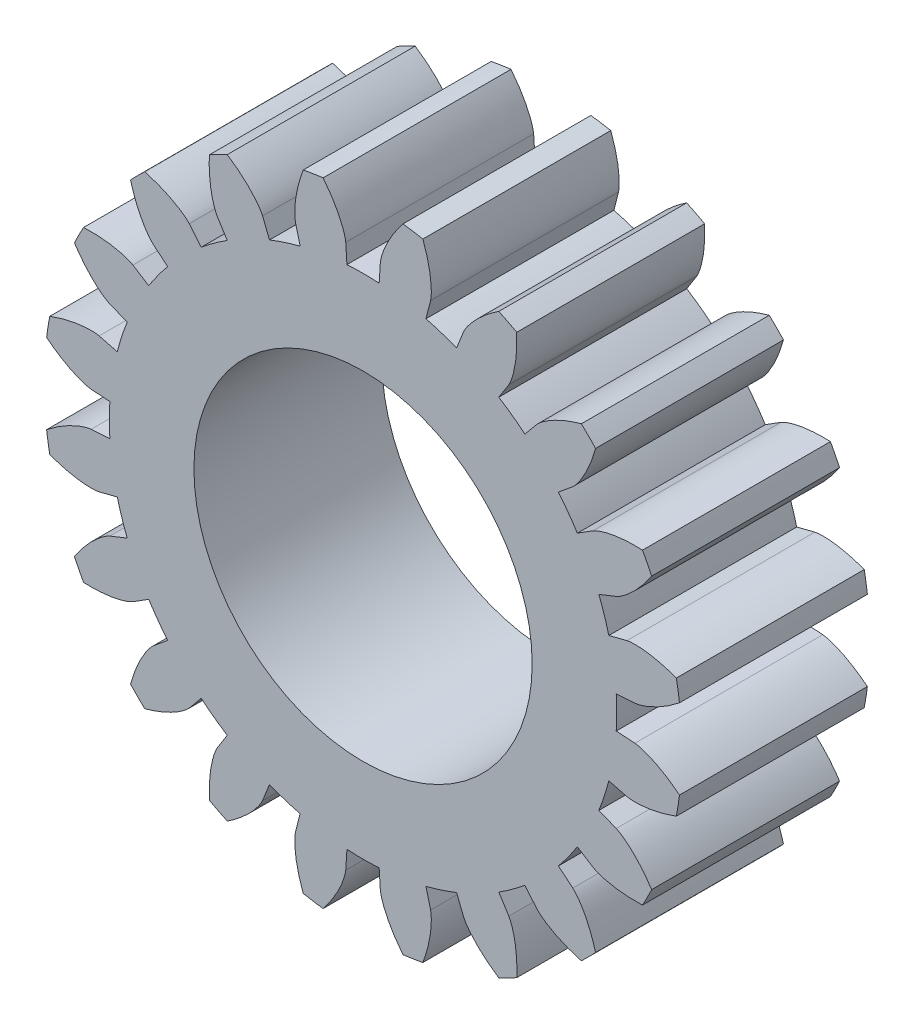
SolidWorks part; units mm, degrees
ref_plane "Front Plane" through (0, 0, 0) normal (0, 0, 1) x (1, 0, 0)
ref_plane "Top Plane" through (0, 0, 0) normal (0, 1, 0) x (1, 0, 0)
ref_plane "Right Plane" through (0, 0, 0) normal (1, 0, 0) x (0, 0, -1)
sketch "Sketch1" plane through (0, 0, 0) normal (0, 0, 1) x (1, 0, 0)
  line L0 (0, 0) -> (0, 16.9725) construction
  line L1 (0, 16.9725) -> (0, 0) construction
  line L2 (0, 0) -> (-16.9725, 0) construction
  circle A0 centre (0, 0) radius 16.9725
  dimension "D1" = 33.945
extrude "Boss-Extrude1" add sketch "Sketch1" along normal blind 10 contours A0
sketch "Sketch3" plane through (0, 0, 10) normal (0, 0, 1) x (1, 0, 0)
  line L0 (0, 0) -> (0, 16.9725) construction
  line L1 (0, 16.9725) -> (0, 0) construction
  line L2 (-16.9725, 0) -> (0, 0) construction
  line L3 (0, 0) -> (-0.9209, 14.4674) construction
  line L4 (0, 0) -> (-2.4281, 14.2919) construction
  line L5 (-2.4281, 14.2919) -> (-0.9314, 14.5462) construction
  line L6 (0, 0) -> (-3.9087, 13.9598) construction
  line L7 (-3.9087, 13.9598) -> (-0.9848, 14.7785) construction
  line L8 (-5.3465, 13.4747) -> (0, 0) construction
  line L9 (0, 0) -> (-5.3465, 13.4747) construction
  line L10 (-5.3465, 13.4747) -> (-1.113, 15.1545) construction
  line L11 (0, 0) -> (-6.7257, 12.8421) construction
  line L12 (-6.7257, 12.8421) -> (-1.3461, 15.6595) construction
  line L13 (0, 0) -> (-8.0312, 12.0687) construction
  line L14 (-8.0312, 12.0687) -> (-1.7117, 16.2741) construction
  line L15 (0, 0) -> (-9.2487, 11.1631) construction
  line L16 (-9.2487, 11.1631) -> (-2.2344, 16.9746) construction
  line L17 (0, 0) -> (-10.3649, 10.1352) construction
  line L18 (-10.3649, 10.1352) -> (-2.9351, 17.7335) construction
  circle A0 centre (0, 0) radius 16.9725 construction
  circle A1 centre (0, 0) radius 14.4967 construction
  circle A2 centre (0, 0) radius 15.4286 construction
  arc A3 (0.5713, 14.5148) -> (-0.9209, 14.4674) centre (0.5713, -8.9752) ccw construction
  arc A4 (0.9209, 14.4674) -> (-0.9209, 14.4674) centre (0, 0) ccw
  arc A5 (-2.9351, 17.7335) -> (2.9351, 17.7335) centre (0, 1.0167) cw
  spline S0 degree 3 poles (-0.9209, 14.4674) (-0.9317, 14.5729) (-0.9862, 14.8058) (-1.125, 15.2067) (-1.3613, 15.7115) (-1.9072, 16.6215) (-2.4816, 17.2888) (-2.9351, 17.7335) knots 0 0 0 0 0.081636 0.183677 0.326533 0.510206 1 1 1 1
  spline S1 degree 3 poles (0.9209, 14.4674) (0.9317, 14.5729) (0.9862, 14.8058) (1.125, 15.2067) (1.3613, 15.7115) (1.9072, 16.6215) (2.4816, 17.2888) (2.9351, 17.7335) knots 0 0 0 0 0.081636 0.183677 0.326533 0.510206 1 1 1 1
  point P13 (-1.2096, 15.3811)
  point P43 (-0.6565, 9.8523)
  dimension "D18" = 30.8571
  dimension "D2" = 28.9933
  dimension "D3" = 1.2096
  dimension "D4" = 6
  dimension "D5" = 1.5182
  dimension "D6" = 6
  dimension "D7" = 3.0363
  dimension "D8" = 4.5545
  dimension "D9" = 6
  dimension "D10" = 6.0727
  dimension "D11" = 6
  dimension "D12" = 6
  dimension "D13" = 7.5909
  dimension "D14" = 6
  dimension "D15" = 9.109
  dimension "D16" = 6
  dimension "D17" = 10.6272
extrude "Cut-Extrude1" cut sketch "Sketch3" against normal blind 10
sketch "Sketch5" plane through (0, 0, 10) normal (0, 0, 1) x (1, 0, 0)
  line L0 (-0.9209, 14.4674) -> (0, 0)
  line L1 (0, 0) -> (0.9209, 14.4674)
  arc A0 (0.9209, 14.4674) -> (-0.9209, 14.4674) centre (0, 0) ccw construction
  arc A1 (0.9209, 14.4674) -> (-0.9209, 14.4674) centre (0, 0) ccw
  circle A2 centre (0, 0) radius 13.5
  arc M7 (0.9209, 14.4674) -> (-0.9209, 14.4674) centre (0, 0) ccw
  dimension "D1" = 27
extrude "Cut-Extrude2" cut sketch "Sketch5" against normal blind 10 contours A2 L1 L0 M7
pattern_circular "CirPattern1" count 20 over 360 about axis through (0, 0, 10) along (0, 0, -1) of "Cut-Extrude1", "Cut-Extrude2"
sketch "Sketch7" plane through (0, 0, 10) normal (0, 0, 1) x (1, 0, 0)
  circle A0 centre (0, 0) radius 9
  dimension "D1" = 18
extrude "Cut-Extrude3" cut sketch "Sketch7" against normal blind 10 contours A0
sketch "Sketch6" plane through (0, 0, 10) normal (0, 0, 1) x (1, 0, 0)
  line L1 (-2.5, 5) -> (2.5, 5)
  line L2 (-2.5, 5) -> (-2.5, 15)
  line L3 (-2.5, 15) -> (2.5, 15)
  line L4 (2.5, 5) -> (2.5, 15)
  line L5 (-2.5, 5) -> (2.5, 15) construction
  line L6 (-2.5, 15) -> (2.5, 5) construction
  circle A0 centre (0, 0) radius 10
  point P3 (0, 10)
  dimension "D1" = 20
  dimension "D2" = 5
  dimension "D3" = 5
equation "\"D7@Sketch3\"=\"D5@Sketch3\"*2"
equation "\"D8@Sketch3\"=\"D5@Sketch3\"*3"
equation "\"D10@Sketch3\"=\"D5@Sketch3\"*4"
equation "\"D13@Sketch3\"=\"D5@Sketch3\"*5"
equation "\"D15@Sketch3\"=\"D5@Sketch3\"*6"
equation "\"D17@Sketch3\"=\"D5@Sketch3\"*7"
